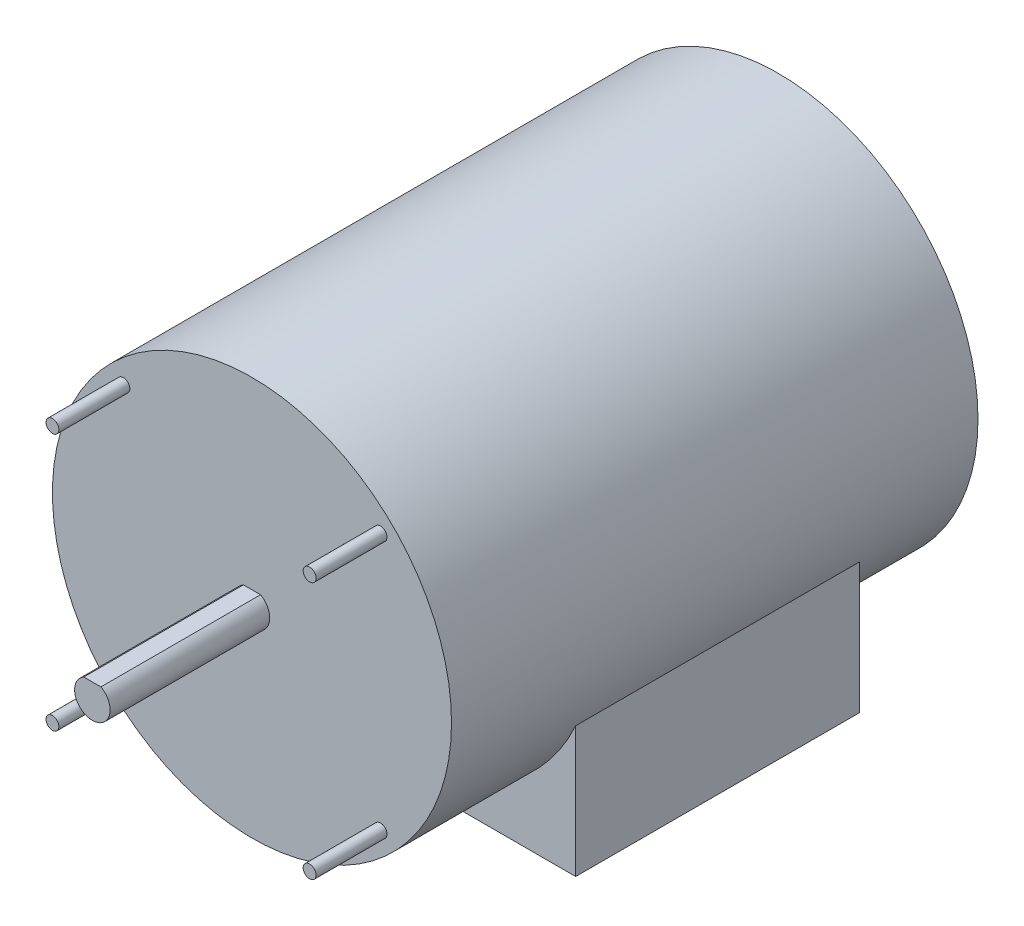
SolidWorks part; units mm, degrees
ref_plane "Front Plane" through (0, 0, 0) normal (0, 0, 1) x (1, 0, 0)
ref_plane "Top Plane" through (0, 0, 0) normal (0, 1, 0) x (1, 0, 0)
ref_plane "Right Plane" through (0, 0, 0) normal (1, 0, 0) x (0, 0, -1)
sketch "Sketch1" plane through (0, 0, 0) normal (0, 0, 1) x (1, 0, 0)
  circle A0 centre (0, 0) radius 71.4375
  dimension "D1" = 142.875
extrude "Boss-Extrude1" add sketch "Sketch1" along normal blind 188.4934
sketch "Sketch2" plane through (0, 0, 188.4934) normal (0, 0, 1) x (1, 0, 0)
  line L0 (78.5813, 0) -> (-78.5813, 0) construction
  line L2 (0, -78.5813) -> (0, 78.5813) construction
  circle A0 centre (-46.0375, 46.0375) radius 2.3082
  circle A1 centre (-46.0375, -46.0375) radius 2.3082
  circle A2 centre (46.0375, -46.0375) radius 2.3082
  circle A3 centre (46.0375, 46.0375) radius 2.3082
  dimension "D3" = 4.6164
  dimension "D1" = 46.0375
  dimension "D2" = 46.0375
extrude "Boss-Extrude2" add sketch "Sketch2" along normal blind 25.4
sketch "Sketch3" plane through (0, 0, 188.4934) normal (0, 0, 1) x (1, 0, 0)
  line L0 (-3.0627, 5.5626) -> (3.0627, 5.5626)
  arc A0 (-3.0627, 5.5626) -> (3.0627, 5.5626) centre (0, 0) ccw
  dimension "D1" = 12.7
  dimension "D2" = 5.5626
extrude "Boss-Extrude3" add sketch "Sketch3" along normal blind 57.15
sketch "Sketch4" plane through (0, 0, 0) normal (0, 1, 0) x (1, 0, 0)
  line L0 (-71.4375, -188.4934) -> (71.4375, -188.4934) construction
  line L1 (65.0875, -137.6934) -> (-65.0875, -137.6934)
  line L2 (65.0875, -137.6934) -> (65.0875, -36.0934)
  line L3 (65.0875, -36.0934) -> (-65.0875, -36.0934)
  line L4 (-65.0875, -137.6934) -> (-65.0875, -36.0934)
  line L5 (65.0875, -137.6934) -> (-65.0875, -36.0934) construction
  line L6 (65.0875, -36.0934) -> (-65.0875, -137.6934) construction
  line L7 (0, -78.5813) -> (0, 78.5813) construction
  line L8 (65.0875, -86.8934) -> (-65.0875, -86.8934) construction
  circle A0 centre (53.975, -121.8184) radius 4.3688
  circle A1 centre (-53.975, -121.8184) radius 4.3688
  circle A2 centre (-53.975, -51.9684) radius 4.3688
  circle A3 centre (53.975, -51.9684) radius 4.3688
  point P0 (0, -86.8934)
  dimension "D6" = 8.7376
  dimension "D1" = 130.175
  dimension "D2" = 50.8
  dimension "D3" = 53.975
  dimension "D4" = 34.925
  dimension "D5" = 101.6
extrude "Boss-Extrude4" add sketch "Sketch4" against normal blind 76.2 contours L4 L1 L2 L3 A1 A0 A2 A3
